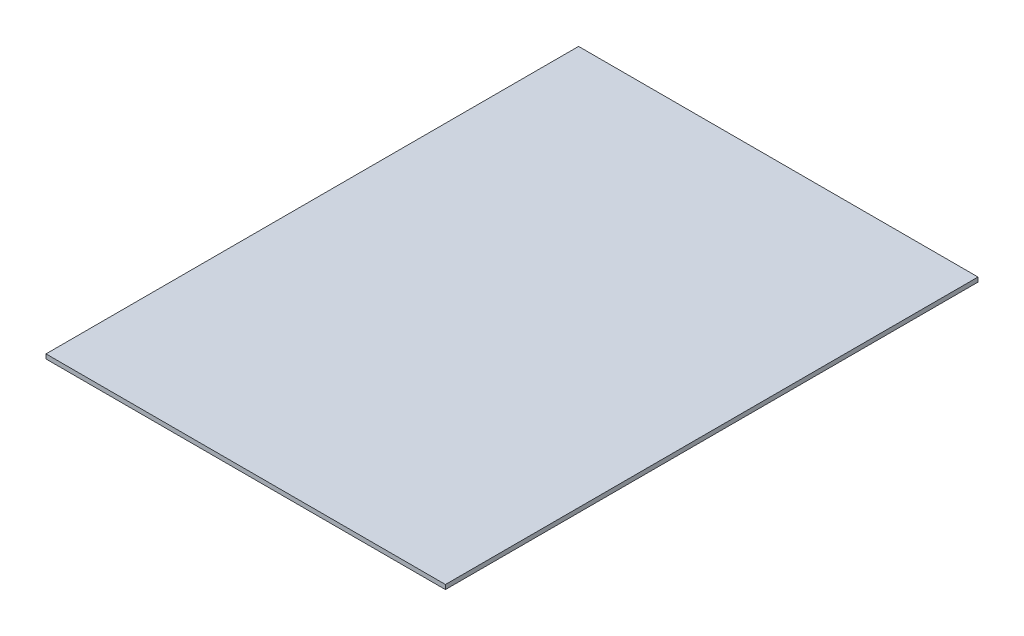
SolidWorks part; units mm, degrees
ref_plane "Front Plane" through (0, 0, 0) normal (0, 0, 1) x (1, 0, 0)
ref_plane "Top Plane" through (0, 0, 0) normal (0, 1, 0) x (1, 0, 0)
ref_plane "Right Plane" through (0, 0, 0) normal (1, 0, 0) x (0, 0, -1)
sketch "Sketch1" plane through (0, 0, 0) normal (0, 1, 0) x (1, 0, 0)
  line L1 (45, -60) -> (-45, -60)
  line L2 (45, -60) -> (45, 60)
  line L3 (45, 60) -> (-45, 60)
  line L4 (-45, -60) -> (-45, 60)
  line L5 (45, -60) -> (-45, 60) construction
  line L6 (45, 60) -> (-45, -60) construction
  point P0 (0, 0)
  dimension "D1" = 90
  dimension "D2" = 120
extrude "Boss-Extrude1" add sketch "Sketch1" along normal blind 1
